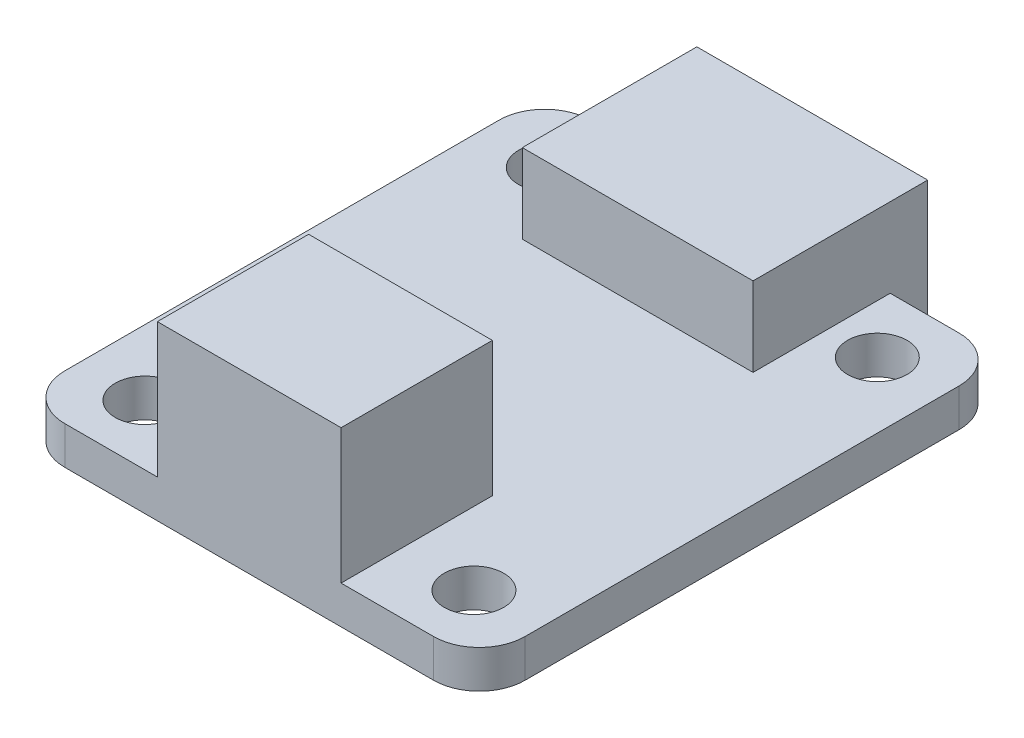
SolidWorks part; units mm, degrees
ref_plane "Front Plane" through (0, 0, 0) normal (0, 0, 1) x (1, 0, 0)
ref_plane "Top Plane" through (0, 0, 0) normal (0, 1, 0) x (1, 0, 0)
ref_plane "Right Plane" through (0, 0, 0) normal (1, 0, 0) x (0, 0, -1)
sketch "Sketch1" plane through (0, 0, 0) normal (0, 1, 0) x (1, 0, 0)
  line L1 (-10.07, 11.679) -> (10.07, 11.679)
  line L2 (-10.07, 11.679) -> (-10.07, -11.321)
  line L3 (-10.07, -11.321) -> (10.07, -11.321)
  line L4 (10.07, 11.679) -> (10.07, -11.321)
  point P4 (0, 11.679)
  dimension "D1" = 23
  dimension "D2" = 20.14
extrude "Boss-Extrude1" add sketch "Sketch1" along normal blind 1.66
sketch "Sketch2" plane through (0, 0, 0) normal (0, -1, 0) x (1, 0, 0)
  line L0 (-10.07, 11.321) -> (10.07, 11.321) construction
  line L1 (-4.02, 11.321) -> (4.02, 11.321)
  line L2 (-4.02, 11.321) -> (-4.02, 4.701)
  line L3 (-4.02, 4.701) -> (4.02, 4.701)
  line L4 (4.02, 11.321) -> (4.02, 4.701)
  line L5 (-10.07, 11.321) -> (10.07, 11.321) construction
  point P6 (0, 11.321)
  point P9 (0, 11.321)
  dimension "D1" = 8.04
  dimension "D2" = 6.62
extrude "Boss-Extrude2" add sketch "Sketch2" against normal blind 7.55
sketch "Sketch3" plane through (0, 0, 0) normal (0, -1, 0) x (1, 0, 0)
  line L0 (10.07, -11.679) -> (-10.07, -11.679) construction
  line L1 (5.05, -13.319) -> (-5.05, -13.319)
  line L2 (5.05, -13.319) -> (5.05, -5.679)
  line L3 (5.05, -5.679) -> (-5.05, -5.679)
  line L4 (-5.05, -13.319) -> (-5.05, -5.679)
  point P6 (0, -5.679)
  dimension "D1" = 10.1
  dimension "D2" = 6
  dimension "D3" = 7.64
extrude "Boss-Extrude3" add sketch "Sketch3" against normal blind 5.13
fillet "Fillet1" radius 2 4 edges at (-10.07, 0.83, -11.679) (-10.07, 0.83, 11.321) (10.07, 0.83, -11.679) (10.07, 0.83, 11.321)
hole_wizard "Hole1" positions "Sketch6" profile "Sketch7" legacy end condition through all
sketch "Sketch6" plane through (0, 1.66, 0) normal (0, 1, 0) x (1, 0, 0)
  line L1 (7.2, -8.6865) -> (-7.2, -8.6865)
  line L2 (7.2, -8.6865) -> (7.2, 8.9659)
  line L3 (7.2, 8.9659) -> (-7.2, 8.9659)
  line L4 (-7.2, -8.6865) -> (-7.2, 8.9659)
  line L5 (0, -8.6865) -> (0, 8.9659) construction
  point P0 (-7.2, 8.9659)
  point P2 (7.2, 8.9659)
  point P4 (7.2, -8.6865)
  point P6 (-7.2, -8.6865)
sketch "Sketch7" plane through (-7.2, 1.66, -8.9659) normal (1, 0, 0) x (0, 0, 1)
  line L0 (0, 0) -> (0, 1.66)
  line L1 (0, 1.66) -> (1.3, 1.66)
  line L2 (1.3, 1.66) -> (1.3, 0)
  line L3 (1.3, 0) -> (0, 0)
  line L4 (0, 110) -> (0, -10) construction
  dimension "Diameter" = 2.6
  dimension "Depth" = 1.66
